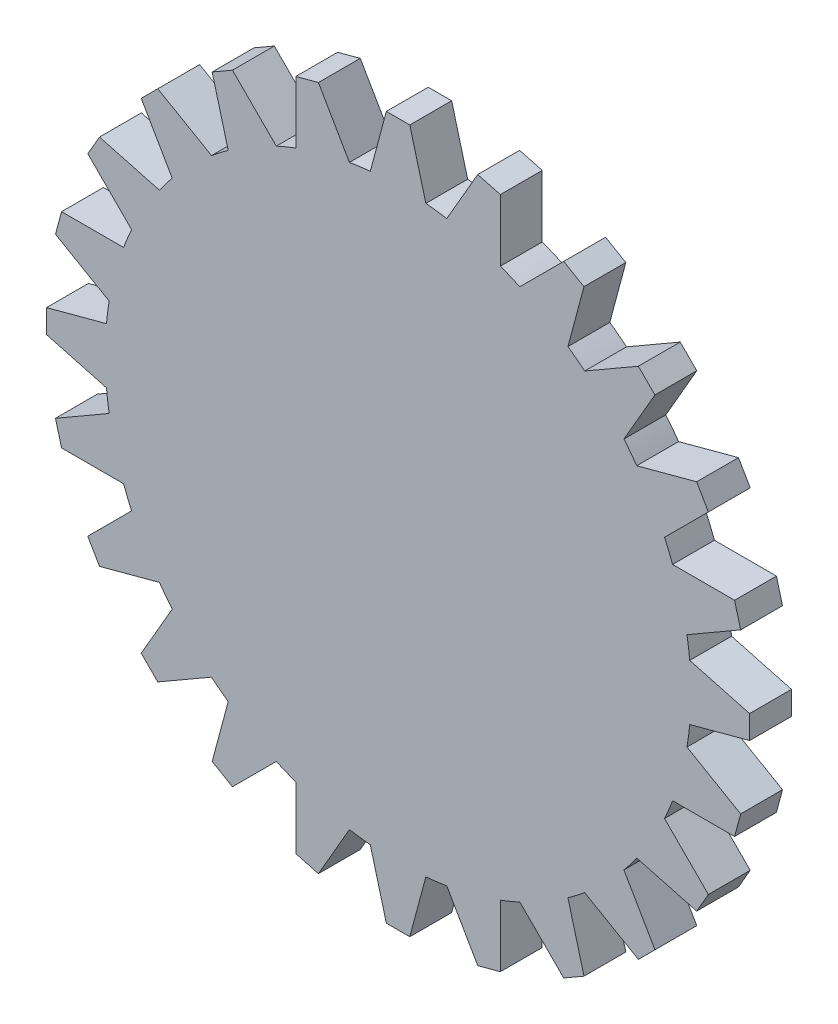
SolidWorks part; units mm, degrees
ref_plane "Front Plane" through (0, 0, 0) normal (0, 0, 1) x (1, 0, 0)
ref_plane "Top Plane" through (0, 0, 0) normal (0, 1, 0) x (1, 0, 0)
ref_plane "Right Plane" through (0, 0, 0) normal (1, 0, 0) x (0, 0, -1)
sketch "Sketch1" plane through (0, 0, 0) normal (0, 0, 1) x (1, 0, 0)
  circle A0 centre (0, 0) radius 7
extrude "Boss-Extrude1" add sketch "Sketch1" along normal blind 1
sketch "Sketch2" plane through (0, 0, 0) normal (0, 0, 1) x (1, 0, 0)
  line L0 (0, 0) -> (0, 8.4) construction
  line L1 (0, 6.72) -> (-0.7302, 6.72)
  line L2 (-0.7302, 6.72) -> (-0.28, 8.4)
  line L3 (-0.28, 8.4) -> (0.28, 8.4)
  line L4 (0.28, 8.4) -> (0.7302, 6.72)
  line L5 (0, 6.72) -> (0.7302, 6.72)
  point P5 (0, 0)
  point P9 (0, 0)
  dimension "D1" = 0.28
  dimension "D2" = 0.28
  dimension "D3" = 6.72
  dimension "D4" = 8.4
  dimension "D5" = 75
  dimension "D6" = 75
extrude "Boss-Extrude2" add sketch "Sketch2" along normal blind 1
pattern_circular "CirPattern1" count 24 every 15 about axis through (0, 0, 0) along (0, 0, 1) of "Boss-Extrude2"
